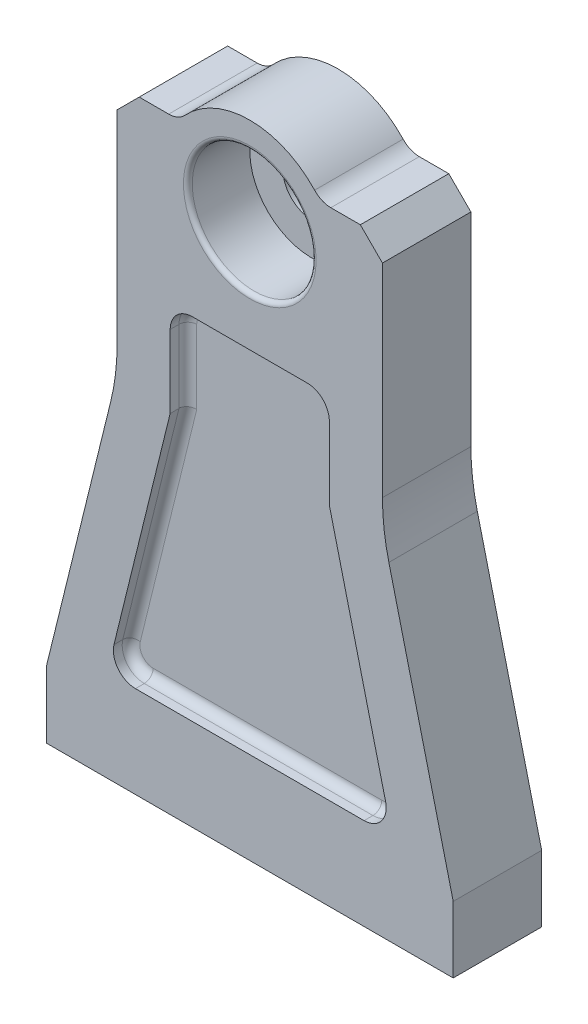
SolidWorks part; units mm, degrees
ref_plane "Front Plane" through (0, 0, 0) normal (0, 0, 1) x (1, 0, 0)
ref_plane "Top Plane" through (0, 0, 0) normal (0, 1, 0) x (1, 0, 0)
ref_plane "Right Plane" through (0, 0, 0) normal (1, 0, 0) x (0, 0, -1)
sketch "Sketch2" plane through (0, 0, 0) normal (0, 0, 1) x (1, 0, 0)
  line L0 (-18.3303, 12) -> (-30, 12)
  line L1 (-30, 12) -> (-30, -38.9367)
  line L2 (-31.4493, -50.8876) -> (-46, -110)
  line L3 (-46, -110) -> (-46, -125)
  line L4 (-46, -125) -> (46, -125)
  line L5 (46, -125) -> (46, -110)
  line L6 (46, -110) -> (31.4493, -50.8876)
  line L7 (30, -38.9367) -> (30, 12)
  line L8 (30, 12) -> (18.3303, 12)
  arc A0 (-14.6642, 13.6) -> (14.6642, 13.6) centre (0, 0) cw
  arc A1 (14.6642, 13.6) -> (18.3303, 12) centre (18.3303, 17) ccw
  arc A2 (-14.6642, 13.6) -> (-18.3303, 12) centre (-18.3303, 17) cw
  arc A3 (31.4493, -50.8876) -> (30, -38.9367) centre (80, -38.9367) cw
  arc A4 (-30, -38.9367) -> (-31.4493, -50.8876) centre (-80, -38.9367) cw
  circle A5 centre (0, 0) radius 6.5
  point P15 (16, 12)
  point P18 (-16, 12)
  point P21 (30, -45)
  point P24 (-30, -45)
  dimension "D1" = 20
  dimension "D7" = 5
  dimension "D8" = 50
  dimension "D10" = 13
  dimension "D2" = 60
  dimension "D3" = 12
  dimension "D4" = 15
  dimension "D5" = 65
  dimension "D6" = 125
  dimension "D9" = 92
extrude "Boss-Extrude1" add sketch "Sketch2" along normal mid plane 20
hole_wizard "M10x1.25 Tapped Hole1" positions "Sketch6" profile "Sketch7" tap size "M10x1.25" standard "ISO"
sketch "Sketch6" plane through (0, -125, 0) normal (0, -1, 0) x (-1, 0, 0)
  point P0 (30, 0)
  point P2 (-30, 0)
  dimension "D1" = 60
  dimension "D2" = 30
sketch "Sketch7" plane through (-30, -125, 0) normal (1, 0, 0) x (0, 0, -1)
  line L0 (0, 0) -> (0, 22.6438)
  line L1 (0, 22.6438) -> (4.4, 20)
  line L2 (4.4, 20) -> (4.4, 0)
  line L5 (4.4, 0) -> (0, 0)
  line L10 (0, 22.6438) -> (-4.4, 20) construction
  line L11 (0, -6.35) -> (0, 107.95) construction
  dimension "Tap Drill Dia." = 8.8
  dimension "Tap Drill Depth" = 20
  dimension "Drill Angle" = 118
cosmetic thread "Hole Thread1" parameters "D1"=20, "D2"=10
cosmetic thread "Hole Thread2" parameters "D1"=20, "D2"=10
sketch "Sketch8" plane through (0, 0, 10) normal (0, 0, 1) x (1, 0, 0)
  circle A0 centre (0, 0) radius 14
  dimension "D1" = 28
extrude "Cut-Extrude1" cut sketch "Sketch8" against normal blind 14
fillet "Fillet1" radius 1 1 edges at (14, 0, 10)
sketch "Sketch9" plane through (0, 0, 10) normal (0, 0, 1) x (1, 0, 0)
  line L0 (-30.704, -98.0651) -> (-18, -46.4552)
  line L1 (-18, -46.4552) -> (-18, -30)
  line L2 (-13, -25) -> (13, -25)
  line L3 (18, -30) -> (18, -46.4552)
  line L4 (18, -46.4552) -> (30.704, -98.0651)
  line L5 (25.8489, -104.2602) -> (-25.8489, -104.2602)
  line L7 (-31.4493, -50.8876) -> (-46, -110) construction
  line L8 (46, -110) -> (31.4493, -50.8876) construction
  line L9 (-30, 12) -> (-30, -38.9367) construction
  line L11 (-46, -125) -> (46, -125) construction
  arc A0 (-30.704, -98.0651) -> (-25.8489, -104.2602) centre (-25.8489, -99.2602) ccw
  arc A1 (30.704, -98.0651) -> (25.8489, -104.2602) centre (25.8489, -99.2602) cw
  arc A2 (13, -25) -> (18, -30) centre (13, -30) cw
  arc A3 (-18, -30) -> (-13, -25) centre (-13, -30) cw
  point P2 (-25.1183, -105.4433)
  dimension "D5" = 5
  dimension "D1" = 12
  dimension "D2" = 12
  dimension "D3" = 12
  dimension "D4" = 100
extrude "Cut-Extrude2" cut sketch "Sketch9" against normal blind 4
fillet "Fillet2" radius 2 10 edges at (18, -38.2276, 6) (16.5355, -26.4645, 6) (0, -25, 6) (-16.5355, -26.4645, 6) (24.352, -72.2601, 6) (29.7843, -102.3444, 6) (0, -104.2602, 6) (-29.7843, -102.3444, 6) (-18, -38.2276, 6) (-24.352, -72.2601, 6)
mirror "Mirror1" about plane through (0, 0, 0) normal (0, 0, 1) of "Fillet2", "Cut-Extrude2"
chamfer "Chamfer1" distance 5 angle 45 2 edges at (30, 12, 0) (-30, 12, 0)
